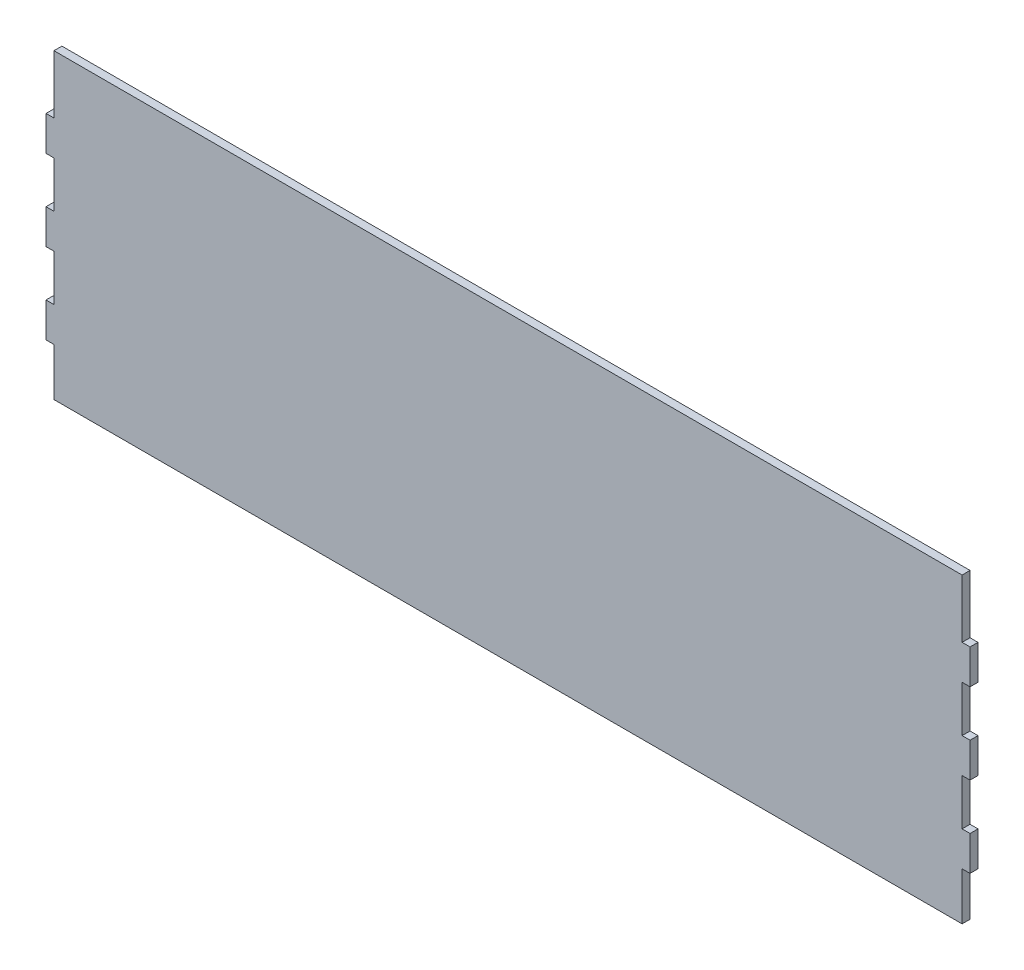
SolidWorks part; units mm, degrees
ref_plane "Front Plane" through (0, 0, 0) normal (0, 0, 1) x (1, 0, 0)
ref_plane "Top Plane" through (0, 0, 0) normal (0, 1, 0) x (1, 0, 0)
ref_plane "Right Plane" through (0, 0, 0) normal (1, 0, 0) x (0, 0, -1)
sketch "Croquis1" plane through (0, 0, 0) normal (0, 0, 1) x (1, 0, 0)
  line L1 (-174.32, 55) -> (174.32, 55)
  line L2 (-174.32, 55) -> (-174.32, -55)
  line L3 (-174.32, -55) -> (174.32, -55)
  line L4 (174.32, 55) -> (174.32, -55)
  line L5 (-174.32, 55) -> (174.32, -55) construction
  line L6 (-174.32, -55) -> (174.32, 55) construction
  point P0 (0, 0)
  dimension "D1" = 348.64
  dimension "D2" = 110
extrude "Saliente-Extruir1" add sketch "Croquis1" along normal blind 3
sketch "Croquis2" plane through (0, 0, 3) normal (0, 0, 1) x (1, 0, 0)
  line L0 (-174.32, 55) -> (-174.32, -55) construction
  line L1 (-174.32, 37) -> (-171.32, 37)
  line L2 (-174.32, 37) -> (-174.32, 23.9518)
  line L3 (-174.32, 23.9518) -> (-171.32, 23.9518)
  line L6 (-174.32, 6.5241) -> (-174.32, -6.5241)
  line L8 (-174.32, 6.5241) -> (-171.32, 6.5241)
  line L10 (-174.32, -6.5241) -> (-171.32, -6.5241)
  line L11 (-174.32, -23.9518) -> (-174.32, -37)
  line L12 (-174.32, -23.9518) -> (-171.32, -23.9518)
  line L14 (-174.32, -37) -> (-171.32, -37)
  line L15 (-174.32, -55) -> (174.32, -55) construction
  line L16 (174.32, 55) -> (-174.32, 55) construction
  line L17 (0, -55) -> (0, 55) construction
  line L18 (174.32, -23.9518) -> (171.32, -23.9518)
  line L19 (-171.32, -52) -> (171.32, -52)
  line L20 (171.32, -52) -> (171.32, 52)
  line L21 (-171.32, 52) -> (-171.32, -52)
  line L22 (171.32, 52) -> (-171.32, 52)
  line L24 (171.32, -52) -> (171.32, -37)
  line L25 (-171.32, 52) -> (-171.32, 37)
  line L28 (174.32, -37) -> (171.32, -37)
  line L29 (174.32, -23.9518) -> (174.32, -37)
  line L30 (174.32, 6.5241) -> (171.32, 6.5241)
  line L32 (174.32, -6.5241) -> (171.32, -6.5241)
  line L33 (174.32, 6.5241) -> (174.32, -6.5241)
  line L34 (174.32, 23.9518) -> (171.32, 23.9518)
  line L36 (174.32, 37) -> (171.32, 37)
  line L37 (174.32, 37) -> (174.32, 23.9518)
  line L38 (-171.32, 23.9518) -> (-171.32, 6.5241)
  line L39 (-171.32, -6.5241) -> (-171.32, -23.9518)
  line L40 (-171.32, -37) -> (-171.32, -52)
  line L41 (171.32, -23.9518) -> (171.32, -6.5241)
  line L42 (171.32, 6.5241) -> (171.32, 23.9518)
  line L43 (171.32, 37) -> (171.32, 52)
  line L44 (-171.32, 52) -> (-171.32, 55)
  line L45 (171.32, 52) -> (171.32, 55)
  line L46 (-171.32, -52) -> (-171.32, -55)
  line L47 (171.32, -52) -> (171.32, -55)
  line L48 (-171.32, -55) -> (171.32, -55)
  line L49 (-171.32, 55) -> (171.32, 55)
  line M3 (174.32, -55) -> (174.32, 55)
  line M4 (174.32, 55) -> (-174.32, 55)
  line M5 (-174.32, 55) -> (-174.32, -55)
  line M6 (-174.32, -55) -> (174.32, -55)
  dimension "D3" = 18
  dimension "D4" = 18
  dimension "D1" = 3
  dimension "D2" = 3
extrude "Cortar-Extruir1" cut sketch "Croquis2" against normal blind 3 contours L25 L44 L1 M4 M5 | L38 L3 L8 M5 | L45 L43 L36 M3 M4 | L42 L30 L34 M3 | L41 L18 L32 M3 | L24 L47 L28 M6 M3 | L39 L10 L12 M5 | L46 L40 L14 M5 M6
sketch "Croquis4" plane through (0, 0, 0) normal (0, 0, -1) x (-1, 0, 0)
  line L6 (171.32, 55) -> (171.32, 37) construction
  line L7 (-171.32, 55) -> (171.32, 55)
  line L8 (-171.32, 55) -> (-171.32, 59)
  line L9 (-171.32, 59) -> (171.32, 59)
  line L10 (171.32, 55) -> (171.32, 59)
  dimension "D1" = 4
extrude "Saliente-Extruir3" add sketch "Croquis4" against normal blind 3
sketch "Croquis6" plane through (0, 0, 0) normal (0, 0, -1) x (-1, 0, 0)
  line L0 (-175, -10.7078) -> (175, -10.7078) construction
  text T0 "ITAM MANTIS" font "Century Gothic" height 25
  point P2 (0, -10.7078)
  dimension "D1" = 350
extrude "Cortar-Extruir4" cut sketch "Croquis6" against normal blind 1.5
